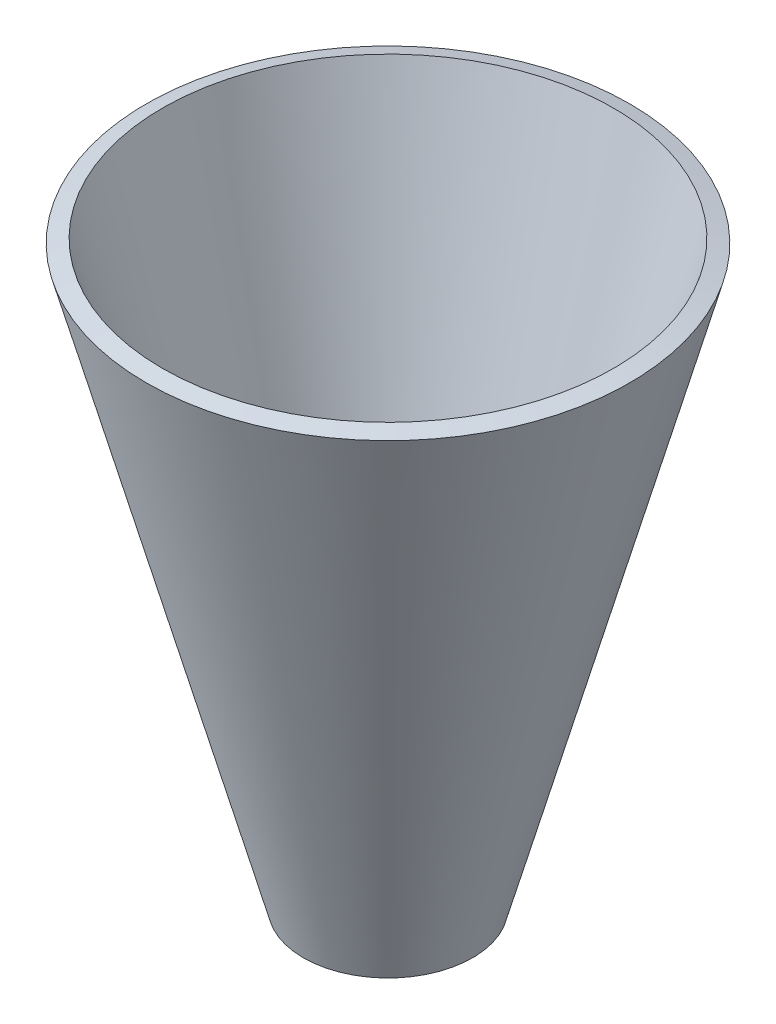
SolidWorks part; units mm, degrees
ref_plane "Ebene vorne" through (0, 0, 0) normal (0, 0, 1) x (1, 0, 0)
ref_plane "Ebene oben" through (0, 0, 0) normal (0, 1, 0) x (1, 0, 0)
ref_plane "Ebene rechts" through (0, 0, 0) normal (1, 0, 0) x (0, 0, -1)
sketch "Skizze1" plane through (0, 0, 0) normal (0, 0, 1) x (1, 0, 0)
  line L0 (0, 35.8192) -> (0, -32.8651) construction
  line L1 (8.1626, -32.8651) -> (26.8723, 35.8192)
revolve "Rotation-Dünn1" add sketch "Skizze1" angle 360 about L0
